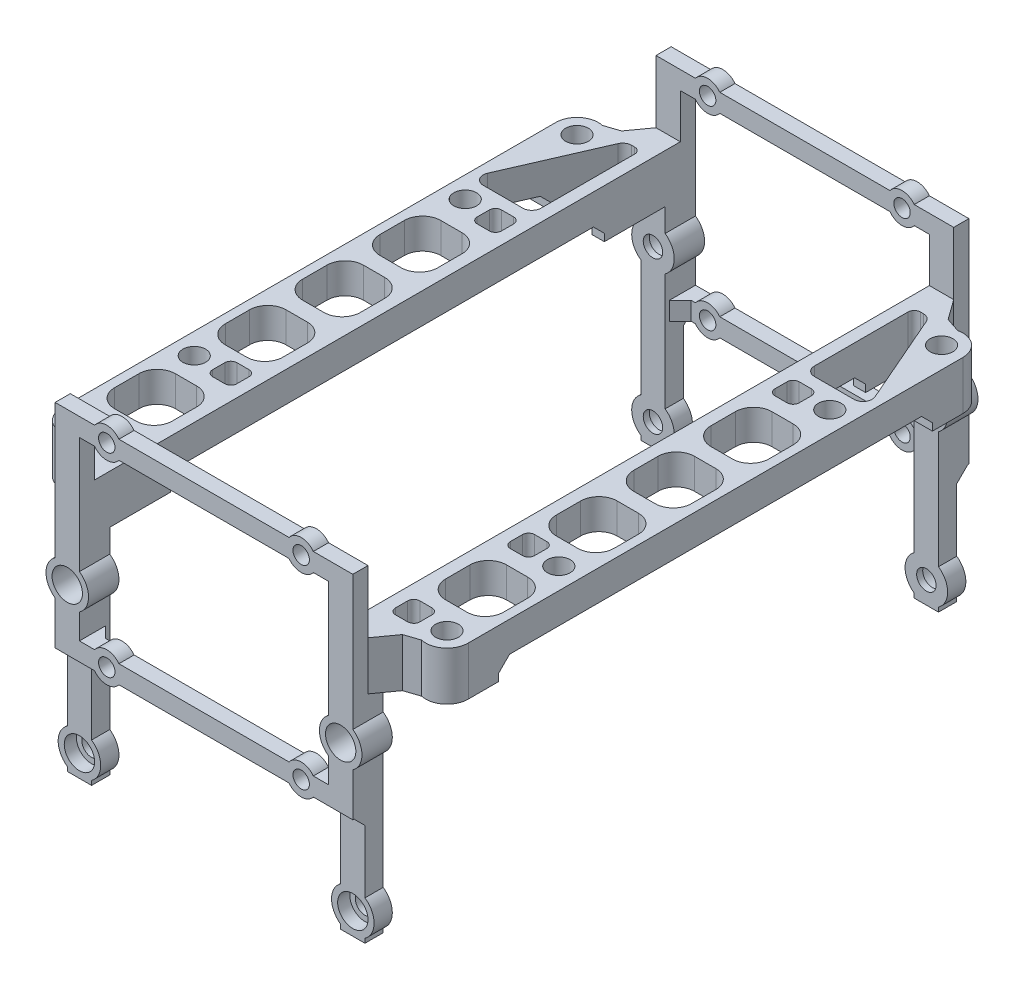
SolidWorks part; units mm, degrees
ref_plane "Front Plane" through (0, 0, 0) normal (0, 0, 1) x (1, 0, 0)
ref_plane "Top Plane" through (0, 0, 0) normal (0, 1, 0) x (1, 0, 0)
ref_plane "Right Plane" through (0, 0, 0) normal (1, 0, 0) x (0, 0, -1)
sketch "Sketch1" plane through (0, 0, 0) normal (1, 0, 0) x (0, 0, -1)
  line L0 (0, 0) -> (-3, 0)
  line L1 (0, 0) -> (91.4, 0) construction
  line L2 (0, 0) -> (0, 35.3)
  line L3 (0, 35.3) -> (91.4, 35.3) construction
  line L4 (91.4, 0) -> (91.4, 35.3)
  line L5 (-3, 0) -> (-3, 43.3)
  line L6 (-3, 43.3) -> (94.4, 43.3) construction
  line L7 (94.4, 43.3) -> (94.4, 0)
  line L8 (94.4, 0) -> (91.4, 0)
  line L9 (45.7, 43.3) -> (45.7, 35.3)
  line L10 (94.4, 43.3) -> (45.7, 43.3)
  line L11 (91.4, 35.3) -> (45.7, 35.3)
  dimension "D1" = 91.4
  dimension "D2" = 35.3
  dimension "D3" = 3
  dimension "D4" = 8
extrude "Boss-Extrude1" add sketch "Sketch1" along normal blind 4 contours L11 L4 L8 L7 L10 L9
sketch "Sketch2" plane through (0, 0, -94.4) normal (0, 0, 1) x (1, 0, 0)
  line L0 (2, 43.3) -> (2, 0) construction
  line L4 (4, 43.3) -> (0, 43.3) construction
  line L5 (4, 35.3) -> (0, 35.3) construction
  line L6 (4, 35.3) -> (0, 35.3) construction
  line L7 (4, 0) -> (0, 0) construction
  circle A0 centre (2, 28.6) radius 1.6
  circle A1 centre (2, 3.6) radius 1.6
  dimension "D1" = 3.2
  dimension "D2" = 25
  dimension "D3" = 6.7
extrude "Cut-Extrude1" cut sketch "Sketch2" along normal through all and the other way through all
sketch "Sketch3" plane through (0, 0, -94.4) normal (0, 0, -1) x (-1, 0, 0)
  line L0 (-2, 28.6) -> (43, 28.6) construction
  line L1 (20.5, 28.6) -> (0, 28.6) construction
  line L2 (6.5, 53.6) -> (20.5, 53.6)
  line L4 (0, 21.6) -> (2.5, 21.6)
  line L5 (20.5, 21.6) -> (20.5, 18.6)
  line L6 (20.5, 18.6) -> (6.5, 18.6)
  line L8 (-2, 3.6) -> (42.5, 3.6) construction
  line L9 (20.5, 20.1) -> (0, 20.1) construction
  line L11 (0, 53.6) -> (0, 50.6) construction
  line L12 (20.5, 50.6) -> (6.5, 50.6)
  line L13 (20.5, 53.6) -> (20.5, 50.6)
  line L14 (0, 53.6) -> (2.5, 53.6)
  line L15 (0, 52.1) -> (20.5, 52.1) construction
  line L16 (-4, 43.3) -> (-4, 53.6)
  line L17 (-4, 53.6) -> (0, 53.6)
  line L18 (-4, 43.3) -> (0, 43.3) construction
  line L19 (0, 43.3) -> (0, 50.6)
  line L20 (4.5, 52.1) -> (4.5, 20.1) construction
  line L21 (0, 21.6) -> (0, 18.6) construction
  line L22 (0, 43.3) -> (0, 0) construction
  line L23 (-4, 43.3) -> (0, 43.3) construction
  line L24 (-4, 43.3) -> (-4, 0) construction
  line L25 (2.5, 50.6) -> (0, 50.6)
  line L26 (6.5, 21.6) -> (20.5, 21.6)
  line L27 (2.5, 18.6) -> (0, 18.6)
  line L28 (-4, 43.3) -> (-4, 31.4723)
  line L29 (-4, 18.6) -> (0, 18.6)
  line L30 (0, 43.3) -> (0, 31.4723)
  line L31 (0, 25.7277) -> (0, 21.6)
  line L32 (-4, 25.7277) -> (-4, 18.6)
  circle A0 centre (4.5, 52.1) radius 1.35
  circle A1 centre (4.5, 20.1) radius 1.35
  arc A2 (2.5, 18.6) -> (6.5, 18.6) centre (4.5, 20.1) ccw
  arc A3 (6.5, 53.6) -> (2.5, 53.6) centre (4.5, 52.1) ccw
  circle A4 centre (-2, 28.6) radius 2.5
  arc A5 (2.5, 50.6) -> (6.5, 50.6) centre (4.5, 52.1) ccw
  arc A6 (6.5, 21.6) -> (2.5, 21.6) centre (4.5, 20.1) ccw
  circle A7 centre (-2, 28.6) radius 3.5
  circle M8 centre (-2, 28.6) radius 1.6
  line M31 (0, 43.3) -> (-4, 43.3)
  line M32 (0, 0) -> (0, 43.3)
  line M33 (-4, 43.3) -> (-4, 0)
  dimension "D5" = 2.7
  dimension "D7" = 5
  dimension "D8" = 5
  dimension "D9" = 7
  dimension "D1" = 45
  dimension "D2" = 3
  dimension "D3" = 15
  dimension "D4" = 32
  dimension "D6" = 16
extrude "Boss-Extrude2" add sketch "Sketch3" against normal blind 0.5 and the other way blind 2 contours L25 A5 L12 L13 L2 A3 L14 L17 L16 L19 A0 M31 | L26 A6 L4 L27 A2 L6 L5 A1 M32 | L29 M33 M32 M31 M8 | A7 M32 M31 M33 | A7 A4 M32 M33 | A7 A4 M32 | A7 A4 M33 | A7 A4 M33 M32
sketch "Sketch4" plane through (0, 0, -94.4) normal (0, 0, -1) x (-1, 0, 0)
  line L0 (20.5, 18.6) -> (20.5, 0) construction
  line L1 (-2, 3.6) -> (20.5, 3.6) construction
  circle A0 centre (-2, 3.6) radius 1.35
  circle A1 centre (-2, 3.6) radius 2.5
  point P8 (0, 0)
sketch "Sketch5" plane through (0, 43.3, 0) normal (0, 1, 0) x (1, 0, 0)
  line L0 (4, 45.7) -> (0, 45.7) construction
  line L1 (2, 45.7) -> (2, 91.4) construction
  line L3 (4, 91.4) -> (8.7463, 89.8179)
  line L4 (13, 86.4) -> (13, 45.7)
  line L5 (9.5, 91.4) -> (9.5, 45.6) construction
  line L8 (4, 91.4) -> (13, 88.4) construction
  line L9 (13, 88.4) -> (13, 45.7) construction
  line L10 (13, 45.7) -> (0, 45.7)
  line L11 (0, 45.7) -> (0, 91.4)
  line L12 (0, 91.4) -> (4, 91.4)
  line L13 (4, 93.9) -> (4, 45.7) construction
  line L14 (0, 93.9) -> (0, 45.7) construction
  line L15 (4, 93.9) -> (4, 45.7) construction
  line L16 (0.4, 91.4) -> (3.6, 91.4) construction
  circle A0 centre (9.5, 86.4) radius 1.875 construction
  arc A2 (13, 86.4) -> (8.7463, 89.8179) centre (9.5, 86.4) ccw
  circle A3 centre (4, 78.4) radius 3.5 construction
  circle A4 centre (4, 69.4) radius 3.5 construction
  circle A5 centre (4, 60.4) radius 3.5 construction
  point P8 (0, 0)
  point P13 (0, 0)
  dimension "D1" = 3.75
  dimension "D6" = 3.5
  dimension "D7" = 7
  dimension "D2" = 5
  dimension "D4" = 3.5
  dimension "D5" = 2
  dimension "D8" = 8
  dimension "D10" = 9
  dimension "D9" = 3
extrude "Boss-Extrude3" add sketch "Sketch5" against normal up to surface (8 mm away) up to face at (2, 35.3, -68.55)
sketch "Sketch9" plane through (0, 0, -94.4) normal (0, 0, -1) x (-1, 0, 0)
  circle A0 centre (4.5, 52.1) radius 1.35
  circle A1 centre (4.5, 52.1) radius 2.5
  circle A2 centre (4.5, 20.1) radius 1.35
  circle A3 centre (4.5, 20.1) radius 2.5
  circle A4 centre (-2, 28.6) radius 1.35
  circle A5 centre (-2, 28.6) radius 3.5
  circle A6 centre (-2, 3.6) radius 1.35 construction
  circle A7 centre (-2, 3.6) radius 1.35
  circle A8 centre (-2, 3.6) radius 2.7378
  arc A9 (6.5, 53.6) -> (2.5, 53.6) centre (4.5, 52.1) ccw construction
  circle A10 centre (4.5, 20.1) radius 2.5 construction
  dimension "D1" = 7
extrude "Boss-Extrude4" [suppressed] add sketch "Sketch9" along normal blind 2 contours A3 | A1 | A0 | A2
sketch "Sketch10" plane through (0, 0, -94.4) normal (0, 0, -1) x (-1, 0, 0)
  circle A0 centre (-2, 28.6) radius 1.6
  circle A1 centre (-2, 28.6) radius 3.5
  circle A2 centre (-2, 3.6) radius 1.6
  circle A3 centre (-2, 3.6) radius 3.5
  circle A4 centre (-2, 3.6) radius 1.6 construction
  circle A5 centre (-2, 28.6) radius 1.6 construction
  dimension "D1" = 7
extrude "Boss-Extrude5" add sketch "Sketch10" against normal up to surface (3 mm away) up to face at (3.6, 28.6, -91.4)
sketch "Sketch11" plane through (0, 0, -94.4) normal (0, 0, -1) x (-1, 0, 0)
  circle A0 centre (-2, 28.6) radius 2.5
  circle A1 centre (-2, 3.6) radius 2.5
  circle A3 centre (-2, 28.6) radius 1.6 construction
  dimension "D1" = 5
extrude "Cut-Extrude4" cut sketch "Sketch11" against normal blind 2
mirror "Mirror4" about plane through (-20.5, 0, -96.4) normal (-1, 0, 0) of bodies 115 108
mirror "Mirror5" about plane through (4, 0, -45.7) normal (0, 0, -1) of bodies 109
sketch "Sketch8" plane through (0, 43.3, 0) normal (0, 1, 0) x (1, 0, 0)
  line L0 (6.5, 34.4749) -> (6.5, 59.4749) construction
  line L1 (5, 50.2415) -> (8.5, 50.2415)
  line L2 (9.5, 86.4) -> (9.5, 5) construction
  line L3 (5, 62.9749) -> (8.5, 62.9749)
  line L6 (2, 88.4) -> (2, 72.9749)
  line L7 (3.5, 71.4749) -> (10, 71.4749)
  line L8 (11.3752, 73.5739) -> (4.8752, 88.4989)
  line L9 (3.5, 89.4) -> (3, 89.4)
  line L10 (0, 93.9) -> (0, -2.5) construction
  line L11 (2, 59.9749) -> (2, 55.9749)
  line L12 (13, 5) -> (13, 86.4) construction
  line L14 (5, 52.9749) -> (8.5, 52.9749)
  line L15 (11.5, 59.9749) -> (11.5, 55.9749)
  line L16 (3, 69.4749) -> (5, 69.4749)
  line L17 (2, 68.4749) -> (2, 66.4749)
  line L18 (3, 65.4749) -> (5, 65.4749)
  line L19 (6, 68.4749) -> (6, 66.4749)
  line L20 (2, 47.2415) -> (2, 43.2415)
  line L21 (5, 40.2415) -> (8.5, 40.2415)
  line L22 (11.5, 47.2415) -> (11.5, 43.2415)
  line L23 (6.5, 21.7415) -> (6.5, 46.7415) construction
  line L24 (5, 37.508) -> (8.5, 37.508)
  line L25 (2, 34.508) -> (2, 30.508)
  line L26 (5, 27.508) -> (8.5, 27.508)
  line L27 (11.5, 34.508) -> (11.5, 30.508)
  line L28 (6.5, 9.008) -> (6.5, 34.008) construction
  line L29 (9.5, 45.7) -> (-6.9785, 45.7) construction
  line L30 (6, 22.9251) -> (6, 24.9251)
  line L31 (3, 25.9251) -> (5, 25.9251)
  line L32 (2, 22.9251) -> (2, 24.9251)
  line L33 (3, 21.9251) -> (5, 21.9251)
  line L34 (9.5, 23.4) -> (-1.2891, 23.4) construction
  line L35 (11.5, 12.292) -> (11.5, 16.292)
  line L36 (5, 19.292) -> (8.5, 19.292)
  line L37 (2, 12.292) -> (2, 16.292)
  line L38 (5, 9.292) -> (8.5, 9.292)
  line L39 (-41, 91.4) -> (0, 91.4) construction
  line L40 (-20.5, 91.4) -> (-20.5, 40.2665) construction
  line L41 (-50.5, 23.4) -> (-39.7109, 23.4) construction
  line L42 (-50.5, 45.7) -> (-34.0215, 45.7) construction
  line L43 (-47.5, 9.008) -> (-47.5, 34.008) construction
  line L44 (-47.5, 21.7415) -> (-47.5, 46.7415) construction
  line L45 (-50.5, 86.4) -> (-50.5, 5) construction
  line L46 (-47.5, 34.4749) -> (-47.5, 59.4749) construction
  line L47 (-46, 9.292) -> (-49.5, 9.292)
  line L48 (-43, 12.292) -> (-43, 16.292)
  line L49 (-46, 19.292) -> (-49.5, 19.292)
  line L50 (-52.5, 12.292) -> (-52.5, 16.292)
  line L51 (-44, 21.9251) -> (-46, 21.9251)
  line L52 (-43, 22.9251) -> (-43, 24.9251)
  line L53 (-44, 25.9251) -> (-46, 25.9251)
  line L54 (-47, 22.9251) -> (-47, 24.9251)
  line L55 (-52.5, 34.508) -> (-52.5, 30.508)
  line L56 (-46, 27.508) -> (-49.5, 27.508)
  line L57 (-43, 34.508) -> (-43, 30.508)
  line L58 (-46, 37.508) -> (-49.5, 37.508)
  line L59 (-52.5, 47.2415) -> (-52.5, 43.2415)
  line L60 (-46, 40.2415) -> (-49.5, 40.2415)
  line L61 (-43, 47.2415) -> (-43, 43.2415)
  line L62 (-47, 68.4749) -> (-47, 66.4749)
  line L63 (-44, 65.4749) -> (-46, 65.4749)
  line L64 (-43, 68.4749) -> (-43, 66.4749)
  line L65 (-44, 69.4749) -> (-46, 69.4749)
  line L66 (-52.5, 59.9749) -> (-52.5, 55.9749)
  line L67 (-46, 52.9749) -> (-49.5, 52.9749)
  line L68 (-43, 59.9749) -> (-43, 55.9749)
  line L69 (-44.5, 89.4) -> (-44, 89.4)
  line L70 (-52.3752, 73.5739) -> (-45.8752, 88.4989)
  line L71 (-44.5, 71.4749) -> (-51, 71.4749)
  line L72 (-43, 88.4) -> (-43, 72.9749)
  line L73 (-46, 62.9749) -> (-49.5, 62.9749)
  line L74 (-46, 50.2415) -> (-49.5, 50.2415)
  line L75 (4, 91.4) -> (5.5, 91.4) construction
  line L76 (0, 93.9) -> (0, -2.5) construction
  line L77 (0, 93.9) -> (4, 93.9) construction
  line L78 (-41, 93.9) -> (-41, -2.5) construction
  line L79 (9.5, 23.4) -> (9.5, 5) construction
  line L80 (6, 3.9694) -> (6, 6.0306)
  line L81 (3, 7.0306) -> (5, 7.0306)
  line L82 (2, 4.0306) -> (2, 6.0306)
  line L83 (3, 3.0306) -> (5, 3.0306)
  line L84 (9.5, 5) -> (6, 5) construction
  line L85 (-44, 3.0306) -> (-46, 3.0306)
  line L86 (-43, 4.0306) -> (-43, 6.0306)
  line L87 (-44, 7.0306) -> (-46, 7.0306)
  line L88 (-47, 3.9694) -> (-47, 6.0306)
  arc A6 (10, 71.4749) -> (11.3752, 73.5739) centre (10, 72.9749) ccw
  arc A7 (2, 72.9749) -> (3.5, 71.4749) centre (3.5, 72.9749) ccw
  arc A8 (4.8752, 88.4989) -> (3.5, 89.4) centre (3.5, 87.9) ccw
  arc A9 (2, 88.4) -> (3, 89.4) centre (3, 88.4) cw
  arc A10 (13, 86.4) -> (8.7463, 89.8179) centre (9.5, 86.4) ccw construction
  arc A11 (13, 86.4) -> (8.7463, 89.8179) centre (9.5, 86.4) ccw construction
  circle A12 centre (9.5, 86.4) radius 1.875
  arc A13 (8.7463, 1.5821) -> (13, 5) centre (9.5, 5) ccw construction
  arc A14 (8.7463, 1.5821) -> (13, 5) centre (9.5, 5) ccw construction
  circle A15 centre (9.5, 5) radius 1.875
  circle A16 centre (9.5, 23.4) radius 1.875
  circle A17 centre (9.5, 68) radius 1.875
  arc A18 (5, 69.4749) -> (6, 68.4749) centre (5, 68.4749) cw
  arc A19 (6, 66.4749) -> (5, 65.4749) centre (5, 66.4749) cw
  arc A20 (3, 65.4749) -> (2, 66.4749) centre (3, 66.4749) cw
  arc A21 (2, 68.4749) -> (3, 69.4749) centre (3, 68.4749) cw
  arc A22 (8.5, 62.9749) -> (11.5, 59.9749) centre (8.5, 59.9749) cw
  arc A23 (11.5, 55.9749) -> (8.5, 52.9749) centre (8.5, 55.9749) cw
  arc A24 (5, 52.9749) -> (2, 55.9749) centre (5, 55.9749) cw
  arc A25 (2, 59.9749) -> (5, 62.9749) centre (5, 59.9749) cw
  arc A26 (8.5, 50.2415) -> (11.5, 47.2415) centre (8.5, 47.2415) cw
  arc A27 (2, 47.2415) -> (5, 50.2415) centre (5, 47.2415) cw
  arc A28 (5, 40.2415) -> (2, 43.2415) centre (5, 43.2415) cw
  arc A29 (11.5, 43.2415) -> (8.5, 40.2415) centre (8.5, 43.2415) cw
  arc A30 (8.5, 37.508) -> (11.5, 34.508) centre (8.5, 34.508) cw
  arc A31 (2, 34.508) -> (5, 37.508) centre (5, 34.508) cw
  arc A32 (5, 27.508) -> (2, 30.508) centre (5, 30.508) cw
  arc A33 (11.5, 30.508) -> (8.5, 27.508) centre (8.5, 30.508) cw
  arc A34 (2, 22.9251) -> (3, 21.9251) centre (3, 22.9251) ccw
  arc A35 (3, 25.9251) -> (2, 24.9251) centre (3, 24.9251) ccw
  arc A36 (6, 24.9251) -> (5, 25.9251) centre (5, 24.9251) ccw
  arc A37 (5, 21.9251) -> (6, 22.9251) centre (5, 22.9251) ccw
  arc A38 (11.5, 16.292) -> (8.5, 19.292) centre (8.5, 16.292) ccw
  arc A39 (5, 19.292) -> (2, 16.292) centre (5, 16.292) ccw
  arc A40 (2, 12.292) -> (5, 9.292) centre (5, 12.292) ccw
  arc A41 (8.5, 9.292) -> (11.5, 12.292) centre (8.5, 12.292) ccw
  arc A42 (-49.7463, 1.5821) -> (-54, 5) centre (-50.5, 5) cw construction
  arc A43 (-54, 86.4) -> (-49.7463, 89.8179) centre (-50.5, 86.4) cw construction
  arc A44 (-49.5, 9.292) -> (-52.5, 12.292) centre (-49.5, 12.292) cw
  arc A45 (-43, 12.292) -> (-46, 9.292) centre (-46, 12.292) cw
  arc A46 (-46, 19.292) -> (-43, 16.292) centre (-46, 16.292) cw
  arc A47 (-52.5, 16.292) -> (-49.5, 19.292) centre (-49.5, 16.292) cw
  arc A48 (-46, 21.9251) -> (-47, 22.9251) centre (-46, 22.9251) cw
  arc A49 (-47, 24.9251) -> (-46, 25.9251) centre (-46, 24.9251) cw
  arc A50 (-44, 25.9251) -> (-43, 24.9251) centre (-44, 24.9251) cw
  arc A51 (-43, 22.9251) -> (-44, 21.9251) centre (-44, 22.9251) cw
  arc A52 (-52.5, 30.508) -> (-49.5, 27.508) centre (-49.5, 30.508) ccw
  arc A53 (-46, 27.508) -> (-43, 30.508) centre (-46, 30.508) ccw
  arc A54 (-43, 34.508) -> (-46, 37.508) centre (-46, 34.508) ccw
  arc A55 (-49.5, 37.508) -> (-52.5, 34.508) centre (-49.5, 34.508) ccw
  arc A56 (-52.5, 43.2415) -> (-49.5, 40.2415) centre (-49.5, 43.2415) ccw
  arc A57 (-46, 40.2415) -> (-43, 43.2415) centre (-46, 43.2415) ccw
  arc A58 (-43, 47.2415) -> (-46, 50.2415) centre (-46, 47.2415) ccw
  arc A59 (-49.5, 50.2415) -> (-52.5, 47.2415) centre (-49.5, 47.2415) ccw
  arc A60 (-43, 59.9749) -> (-46, 62.9749) centre (-46, 59.9749) ccw
  arc A61 (-46, 52.9749) -> (-43, 55.9749) centre (-46, 55.9749) ccw
  arc A62 (-52.5, 55.9749) -> (-49.5, 52.9749) centre (-49.5, 55.9749) ccw
  arc A63 (-49.5, 62.9749) -> (-52.5, 59.9749) centre (-49.5, 59.9749) ccw
  arc A64 (-43, 68.4749) -> (-44, 69.4749) centre (-44, 68.4749) ccw
  arc A65 (-44, 65.4749) -> (-43, 66.4749) centre (-44, 66.4749) ccw
  arc A66 (-47, 66.4749) -> (-46, 65.4749) centre (-46, 66.4749) ccw
  arc A67 (-46, 69.4749) -> (-47, 68.4749) centre (-46, 68.4749) ccw
  circle A68 centre (-50.5, 68) radius 1.875
  circle A69 centre (-50.5, 23.4) radius 1.875
  circle A70 centre (-50.5, 5) radius 1.875
  circle A71 centre (-50.5, 86.4) radius 1.875
  arc A72 (-43, 88.4) -> (-44, 89.4) centre (-44, 88.4) ccw
  arc A73 (-45.8752, 88.4989) -> (-44.5, 89.4) centre (-44.5, 87.9) cw
  arc A74 (-43, 72.9749) -> (-44.5, 71.4749) centre (-44.5, 72.9749) cw
  arc A75 (-51, 71.4749) -> (-52.3752, 73.5739) centre (-51, 72.9749) cw
  arc A76 (2, 4.0306) -> (3, 3.0306) centre (3, 4.0306) ccw
  arc A77 (3, 7.0306) -> (2, 6.0306) centre (3, 6.0306) ccw
  arc A78 (6, 6.0306) -> (5, 7.0306) centre (5, 6.0306) ccw
  arc A79 (5, 3.0306) -> (6, 3.9694) centre (5.0019, 4.0306) ccw
  arc A80 (-46, 3.0306) -> (-47, 3.9694) centre (-46.0019, 4.0306) cw
  arc A81 (-47, 6.0306) -> (-46, 7.0306) centre (-46, 6.0306) cw
  arc A82 (-44, 7.0306) -> (-43, 6.0306) centre (-44, 6.0306) cw
  arc A83 (-43, 4.0306) -> (-44, 3.0306) centre (-44, 4.0306) cw
  dimension "D5" = 1.5
  dimension "D6" = 1
  dimension "D7" = 3.75
  dimension "D8" = 3.75
  dimension "D16" = 63
  dimension "D17" = 63
  dimension "D4" = 1
  dimension "D22" = 3
  dimension "D2" = 25
  dimension "D9" = 0.5
  dimension "D10" = 3
  dimension "D11" = 2
  dimension "D12" = 3.5
  dimension "D13" = 12
  dimension "D14" = 5.5
  dimension "D15" = 6.5
  dimension "D18" = 2
  dimension "D19" = 4
  dimension "D3" = 5
  dimension "D20" = 1.5
  dimension "D21" = 2.5
  dimension "D24" = 10
  dimension "D23" = 3
extrude "Cut-Extrude3" cut sketch "Sketch8" against normal through all
chamfer "Chamfer1" distance 2.5 4 edges at (-45, 39.3, 0) (-45, 39.3, -91.4) (4, 39.3, 0) (4, 39.3, -91.4)
sketch "Sketch12" plane through (0, 35.3, 0) normal (0, -1, 0) x (1, 0, 0)
  line L0 (0, 0) -> (-41, 0) construction
  line L1 (-20.5, 0) -> (-20.5, -83.4352) construction
  line L2 (0, -45.7) -> (-20.5, -45.7) construction
  line L3 (0, -91.4) -> (0, 0) construction
  circle A0 centre (9.5, -5) radius 3
  circle A1 centre (9.5, -23.4) radius 3
  circle A2 centre (9.5, -86.4) radius 3
  circle A3 centre (9.5, -68) radius 3
  circle A4 centre (-50.5, -86.4) radius 3
  circle A5 centre (-50.5, -68) radius 3
  circle A6 centre (-50.5, -23.4) radius 3
  circle A7 centre (-50.5, -5) radius 3
  dimension "D1" = 6
extrude "Cut-Extrude7" cut sketch "Sketch12" against normal blind 4.5
sketch "Sketch13" plane through (-54, 0, 0) normal (-1, 0, 0) x (0, 0, 1)
  line L0 (-45.7, 38.3) -> (-45.7, 43.3) construction
  line L1 (-81.4, 38.3) -> (-10, 38.3)
  line L2 (-81.4, 38.3) -> (-81.4, 30.9146)
  line L3 (-81.4, 30.9146) -> (-10, 30.9146)
  line L4 (-10, 38.3) -> (-10, 30.9146)
  line L5 (-5, 43.3) -> (-86.4, 43.3) construction
  line L6 (-5, 35.3) -> (-5, 43.3) construction
  line L7 (-5, 35.3) -> (-86.4, 35.3) construction
  dimension "D1" = 5
  dimension "D2" = 3
extrude "Cut-Extrude8" cut sketch "Sketch13" against normal through all
chamfer "Chamfer2" distance 1.8 angle 45 4 edges at (-43, 18.6, 3) (2, 18.6, 3) (-43, 18.6, -94.4) (2, 18.6, -94.4)
chamfer "Chamfer3" distance 1.8 angle 45 4 edges at (-41, 20.1, 2.5) (0, 20.1, 2.5) (0, 20.1, -93.9) (-41, 20.1, -93.9)
chamfer "Chamfer4" distance 1.8 angle 45 8 edges at (11.7178, 38.3, -10) (1.5322, 38.3, -10) (10.4834, 38.3, -81.4) (1, 38.3, -81.4) (-42.5322, 38.3, -10) (-52.7178, 38.3, -10) (-42, 38.3, -81.4) (-51.4834, 38.3, -81.4)
